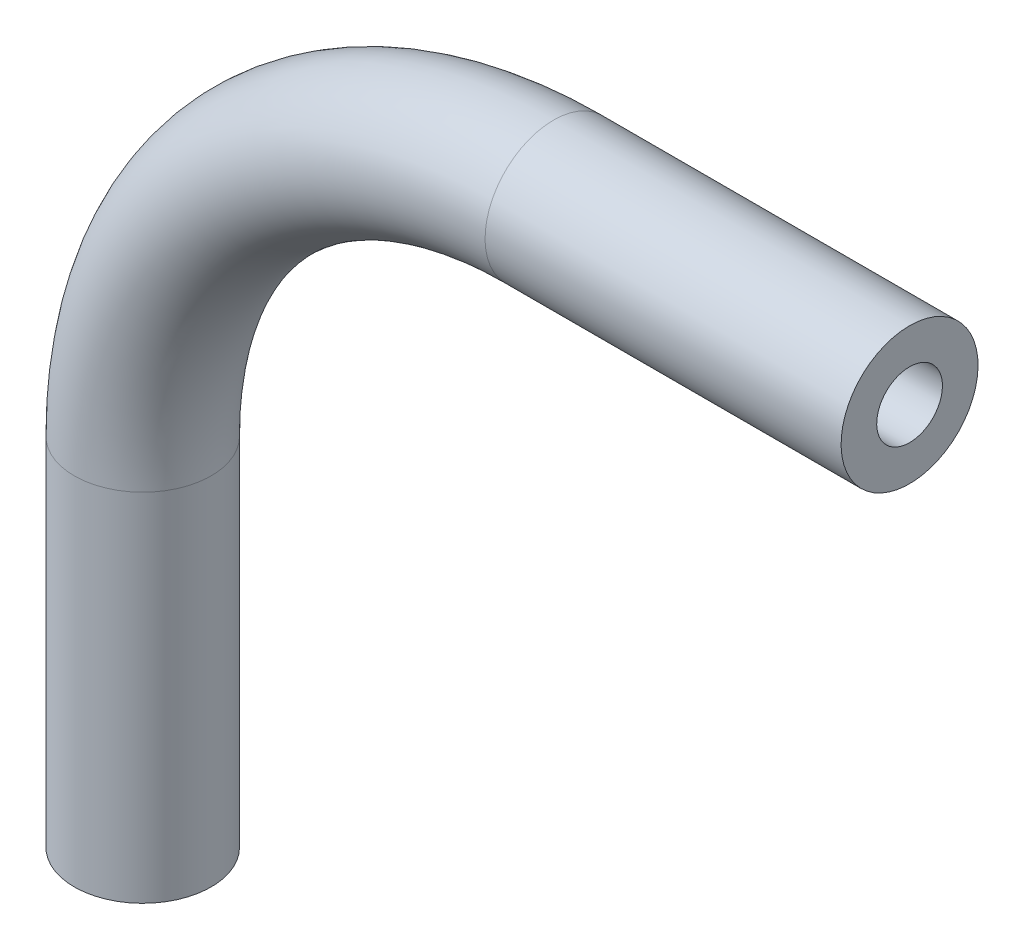
SolidWorks part; units mm, degrees
material "AISI Type 316L stainless steel"
ref_plane "Front Plane" through (0, 0, 0) normal (0, 0, 1) x (1, 0, 0)
ref_plane "Top Plane" through (0, 0, 0) normal (0, 1, 0) x (1, 0, 0)
ref_plane "Right Plane" through (0, 0, 0) normal (1, 0, 0) x (0, 0, -1)
sketch "Sketch1" plane through (0, 0, 0) normal (0, 0, 1) x (1, 0, 0)
  line L0 (0, -18.0323) -> (0, -1.5223)
  line L1 (19.05, 17.5277) -> (35.56, 17.5277)
  arc A0 (0, -1.5223) -> (19.05, 17.5277) centre (19.05, -1.5223) cw
  point P6 (0, 17.5277)
  dimension "D3" = 19.05
  dimension "D1" = 35.56
  dimension "D2" = 35.56
  dimension "D4" = 90
ref_plane "Plane1" through (35.56, 17.5277, 0) normal (1, 0, 0) x (0, 0, -1)
sketch "Sketch2" plane through (35.56, 17.5277, 0) normal (1, 0, 0) x (0, 0, -1)
  circle A0 centre (0, 0) radius 3.175
  circle A1 centre (0, 0) radius 1.524
  dimension "D1" = 6.35
  dimension "D2" = 3.048
sweep "Sweep1" add profiles "Sketch2" path "Sketch1"
